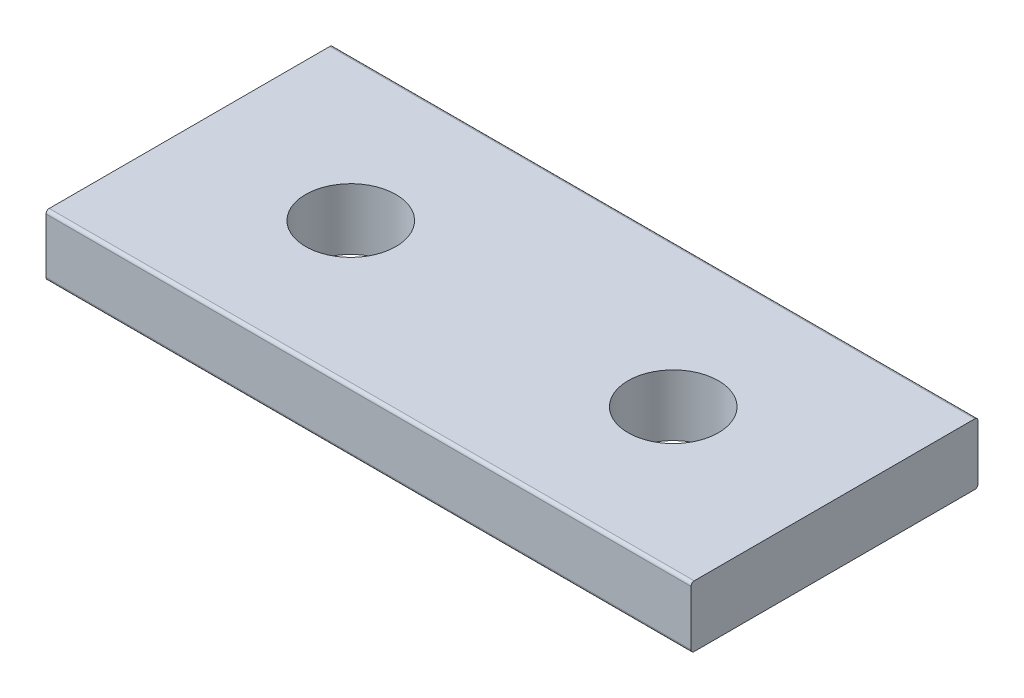
SolidWorks part; units mm, degrees
ref_plane "Front Plane" through (0, 0, 0) normal (0, 0, 1) x (1, 0, 0)
ref_plane "Top Plane" through (0, 0, 0) normal (0, 1, 0) x (1, 0, 0)
ref_plane "Right Plane" through (0, 0, 0) normal (1, 0, 0) x (0, 0, -1)
ref_plane "Plane1" through (0, 1.9, 0) normal (0, 1, 0) x (1, 0, 0)
sketch "Sketch1" plane through (0, 1.9, 0) normal (0, 1, 0) x (1, 0, 0)
  line L0 (20, -8.9) -> (20, 8.9)
  line L1 (20, 8.9) -> (-20, 8.9)
  line L2 (-20, 8.9) -> (-20, -8.9)
  line L3 (-20, -8.9) -> (20, -8.9)
extrude "Boss-Extrude1" add sketch "Sketch1" against normal blind 3.8
hole_wizard "Ø5.6 (5.6) Diameter Hole1" positions "Sketch3" profile "Sketch2" hole size "Ø5.6" standard "ANSI Metric"
sketch "Sketch3" plane through (0, -1.9, 0) normal (0, -1, 0) x (-1, 0, 0)
  point P0 (10, 0)
  point P1 (-10, 0)
sketch "Sketch2" plane through (-10, -1.9, 0) normal (1, 0, 0) x (0, 0, -1)
  line L0 (0, 0) -> (0, 3.8)
  line L1 (0, 3.8) -> (2.8, 3.8)
  line L2 (2.8, 3.8) -> (2.8, 0)
  line L5 (2.8, 0) -> (0, 0)
  line L11 (0, -6.35) -> (0, 107.95) construction
  dimension "Thru Hole Dia." = 5.6
  dimension "Thru Hole Depth" = 3.8
fillet "Fillet1" radius 0.2 4 edges at (0, -1.9, 8.9) (0, 1.9, 8.9) (0, -1.9, -8.9) (0, 1.9, -8.9)
